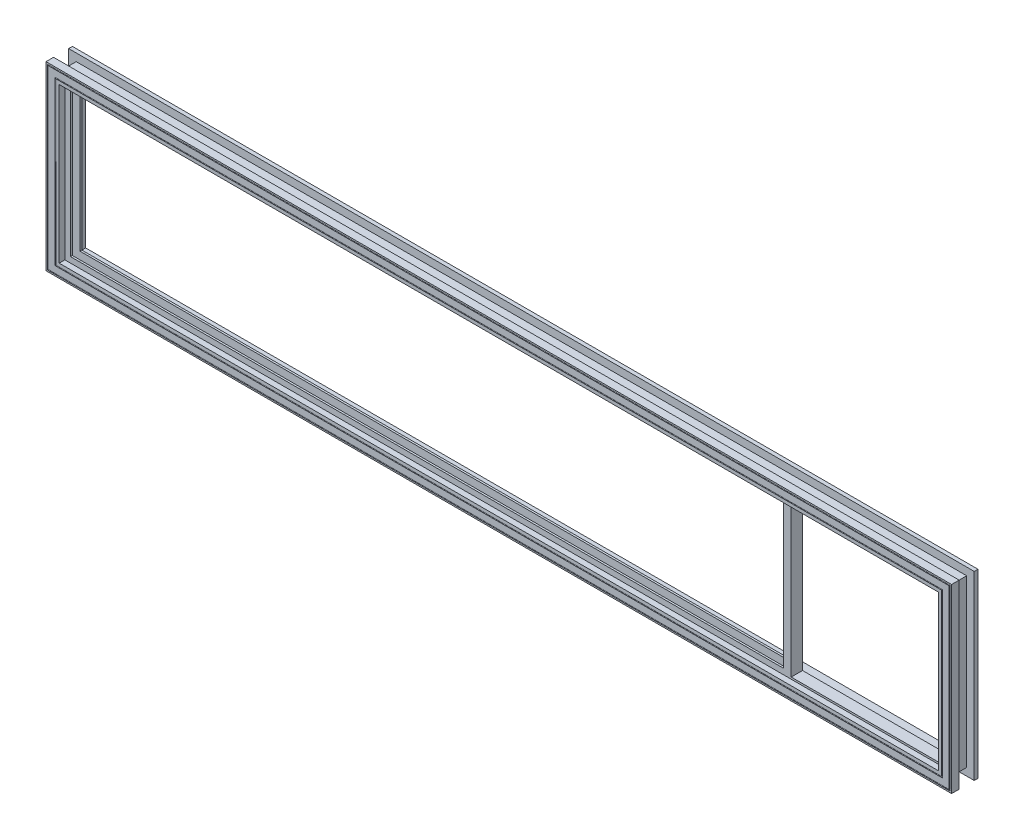
SolidWorks part; units mm, degrees
material "ABS"
ref_plane "Front Plane" through (0, 0, 0) normal (0, 0, 1) x (1, 0, 0)
ref_plane "Top Plane" through (0, 0, 0) normal (0, 1, 0) x (1, 0, 0)
ref_plane "Right Plane" through (0, 0, 0) normal (1, 0, 0) x (0, 0, -1)
sketch "Sketch1" plane through (0, 0, 0) normal (0, 1, 0) x (1, 0, 0)
  line L0 (-762, -25.4) -> (-759.587, -25.4)
  line L1 (-730.25, -15.875) -> (-730.25, -12.7)
  line L2 (-730.25, -12.7) -> (-742.95, -12.7)
  line L3 (-742.95, -12.7) -> (-742.95, 0)
  line L4 (-742.95, 0) -> (-730.25, 0)
  line L5 (-730.25, 0) -> (-730.25, 3.175)
  line L6 (-739.775, 19.05) -> (-745.744, 19.05)
  line L7 (-762, 19.05) -> (-762, 12.7)
  line L8 (-762, 12.7) -> (-749.3, 12.7)
  line L9 (-749.3, 12.7) -> (-749.3, -12.7)
  line L10 (-749.3, -12.7) -> (-762, -12.7)
  line L11 (-762, -12.7) -> (-762, -25.4)
  line L12 (-758.063, -25.4) -> (-746.887, -25.4)
  line L13 (-745.363, -25.4) -> (-739.775, -25.4)
  line L14 (-759.206, 19.05) -> (-762, 19.05)
  line L15 (-746.506, 19.05) -> (-758.444, 19.05)
  line L16 (-739.775, -25.4) -> (-739.775, -15.875)
  line L17 (-739.775, -15.875) -> (-730.25, -15.875)
  line L18 (-739.775, 19.05) -> (-739.775, 3.175)
  line L19 (-739.775, 3.175) -> (-730.25, 3.175)
  arc A0 (-758.063, -25.4) -> (-759.587, -25.4) centre (-758.825, -25.4) ccw
  arc A1 (-745.363, -25.4) -> (-746.887, -25.4) centre (-746.125, -25.4) ccw
  arc A2 (-759.206, 19.05) -> (-758.444, 19.05) centre (-758.825, 19.05) ccw
  arc A3 (-746.506, 19.05) -> (-745.744, 19.05) centre (-746.125, 19.05) ccw
  point P1 (-749.3, 0)
  point P13 (-762, 15.875)
  dimension "D11" = 0.762
  dimension "D12" = 0.762
  dimension "D13" = 0.762
  dimension "D14" = 0.762
  dimension "D1" = 762
  dimension "D2" = 12.7
  dimension "D3" = 44.45
  dimension "D4" = 6.35
  dimension "D5" = 25.4
  dimension "D6" = 12.7
  dimension "D7" = 6.35
  dimension "D8" = 3.175
  dimension "D9" = 12.7
  dimension "D10" = 3.175
  dimension "D15" = 12.7
  dimension "D16" = 3.175
  dimension "D17" = 3.175
  dimension "D18" = 9.525
  dimension "D19" = 31.75
  dimension "D20" = 6.35
sketch "Sketch2" plane through (0, 0, 0) normal (0, 0, 1) x (1, 0, 0)
  line L1 (762, 152.4) -> (-762, 152.4)
  line L2 (762, 152.4) -> (762, -152.4)
  line L3 (762, -152.4) -> (-762, -152.4)
  line L4 (-762, 152.4) -> (-762, -152.4)
  line L5 (762, 152.4) -> (-762, -152.4) construction
  line L6 (762, -152.4) -> (-762, 152.4) construction
  point P0 (0, 0)
  dimension "D1" = 1524
  dimension "D2" = 304.8
sweep "Sweep1" add profiles "Sketch1" path "Sketch2"
sketch "Sketch3" plane through (0, 0, 15.875) normal (0, 0, 1) x (1, 0, 0)
  line L1 (482.6, -127) -> (736.6, -127)
  line L2 (482.6, -127) -> (482.6, 127)
  line L3 (482.6, 127) -> (736.6, 127)
  line L4 (736.6, -127) -> (736.6, 127)
  line L5 (482.6, -127) -> (736.6, 127) construction
  line L6 (482.6, 127) -> (736.6, -127) construction
  line L12 (730.25, 120.65) -> (730.25, -120.65) construction
  line L13 (-730.25, 120.65) -> (730.25, 120.65) construction
  line L14 (730.25, -120.65) -> (-730.25, -120.65) construction
  point P0 (609.6, 0)
  dimension "D1" = 254
  dimension "D2" = 6.35
  dimension "D3" = 6.35
  dimension "D4" = 6.35
extrude "Cut-Extrude1" cut sketch "Sketch3" against normal up to surface (19.05 mm away)
sketch "Sketch6" plane through (0, -133.35, 0) normal (0, 1, 0) x (1, 0, 0)
  line L0 (482.6, 3.175) -> (482.6, -15.875)
  line L1 (482.6, -15.875) -> (469.9, -15.875)
  line L2 (469.9, -15.875) -> (469.9, -12.7)
  line L3 (469.9, -12.7) -> (479.425, -12.7)
  line L4 (479.425, -12.7) -> (479.425, 0)
  line L5 (479.425, 0) -> (469.9, 0)
  line L6 (469.9, 0) -> (469.9, 3.175)
  line L7 (469.9, 3.175) -> (482.6, 3.175)
  line L8 (482.6, 3.175) -> (482.6, 0) construction
  line L9 (739.775, 3.175) -> (-739.775, 3.175) construction
  line L10 (739.775, -15.875) -> (-739.775, -15.875) construction
  line L11 (482.6, 0) -> (-730.25, 0) construction
  line L12 (482.6, -12.7) -> (-730.25, -12.7) construction
  point P10 (482.6, 1.5875)
  dimension "D1" = 3.175
  dimension "D2" = 12.7
extrude "Boss-Extrude1" add sketch "Sketch6" along normal up to surface (266.7 mm away) up to face at (0, 133.35, 6.35)
sketch "Sketch7" plane through (482.6, 0, 0) normal (1, 0, 0) x (0, 0, -1)
  line L0 (-12.7, -127) -> (-15.875, -127) construction
  line L1 (-12.7, -130.175) -> (0, -130.175)
  line L2 (-12.7, -130.175) -> (-12.7, -127)
  line L3 (-12.7, -127) -> (0, -127)
  line L4 (0, -130.175) -> (0, -127)
  line L5 (-12.7, -130.175) -> (0, -127) construction
  line L6 (-12.7, -127) -> (0, -130.175) construction
  line L7 (-12.7, -133.35) -> (-12.7, -127) construction
  line L8 (0, -127) -> (0, -133.35) construction
  point P0 (-6.35, -128.5875)
  dimension "D1" = 3.175
sketch "Sketch8" plane through (0, 0, -3.175) normal (0, 0, -1) x (-1, 0, 0)
  line L0 (-482.6, -127) -> (-736.6, -127)
  line L1 (-736.6, -127) -> (-736.6, 127)
  line L2 (-736.6, -127) -> (-736.6, 127) construction
  line L4 (-482.6, 127) -> (-736.6, 127)
sweep "Sweep2" add profiles "Sketch7" path "Sketch8"
sketch "Sketch9" plane through (739.775, 0, 0) normal (-1, 0, 0) x (0, 0, 1)
  line L0 (20.6375, -130.175) -> (20.6375, 130.175) construction
  line L1 (15.875, -130.175) -> (25.4, -130.175) construction
  line L2 (15.875, 130.175) -> (25.4, 130.175) construction
  line L3 (15.875, 130.175) -> (15.875, -130.175) construction
  dimension "D1" = 4.7625
